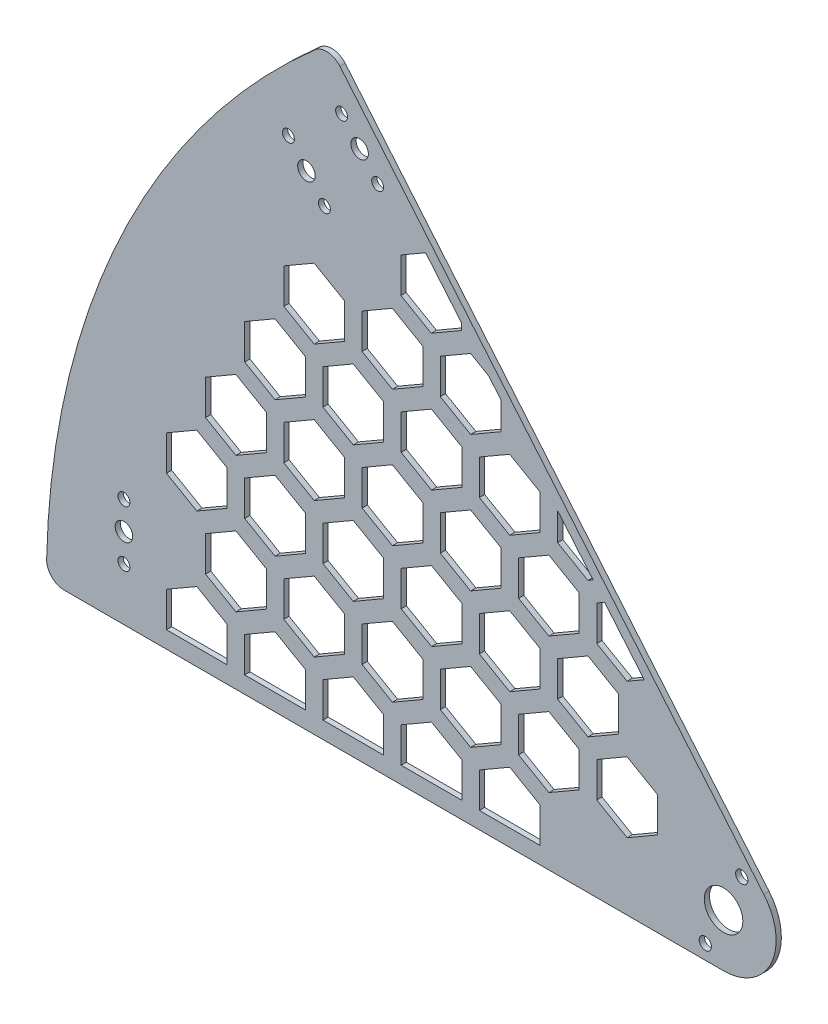
SolidWorks part; units mm, degrees
material "6061 Alloy"
ref_plane "Front Plane" through (0, 0, 0) normal (0, 0, 1) x (1, 0, 0)
ref_plane "Top Plane" through (0, 0, 0) normal (0, 1, 0) x (1, 0, 0)
ref_plane "Right Plane" through (0, 0, 0) normal (1, 0, 0) x (0, 0, -1)
sketch "Sketch1" plane through (0, 0, 0) normal (0, 0, 1) x (1, 0, 0)
  line L0 (22.9813, 19.2836) -> (-218.8588, 307.4975)
  line L1 (0, -30) -> (-376.2365, -30)
  arc A1 (-386.234, -19.7731) -> (-233.1193, 308.5823) centre (64.3352, -30) cw
  circle A2 centre (0, 0) radius 11
  circle A3 centre (0, 0) radius 65 construction
  circle A4 centre (-166.0606, 81.5406) radius 120 construction
  arc A6 (-376.2365, -30) -> (-386.234, -19.7731) centre (-376.2365, -20) cw
  arc A7 (-233.1193, 308.5823) -> (-218.8588, 307.4975) centre (-226.5193, 301.0697) cw
  circle A9 centre (-207.6577, 272.3684) radius 5
  circle A10 centre (0, 0) radius 342.5 construction
  circle A11 centre (-237.9967, 246.3003) radius 5
  circle A12 centre (-342.1261, 16) radius 5
  circle A13 centre (-248.2813, 258.557) radius 3.4 construction
  circle A14 centre (-227.7121, 234.0436) radius 3.4 construction
  circle A15 centre (-197.3731, 260.1117) radius 3.4 construction
  circle A16 centre (-217.9423, 284.6251) radius 3.4 construction
  circle A17 centre (-248.2813, 258.557) radius 3.4
  circle A18 centre (-227.7121, 234.0436) radius 3.4
  circle A19 centre (-197.3731, 260.1117) radius 3.4
  circle A20 centre (-217.9423, 284.6251) radius 3.4
  circle A21 centre (-342.1261, 0) radius 3.4 construction
  circle A22 centre (-342.1261, 32) radius 3.4 construction
  circle A23 centre (-342.1261, 0) radius 3.4
  circle A24 centre (-342.1261, 32) radius 3.4
  arc A27 (-165.8903, -30) -> (-83.6509, 146.363) centre (0, 0) cw construction
  arc A28 (22.9813, 19.2836) -> (0, -30) centre (0, 0) cw
  point P26 (-386.35, -30)
  dimension "D1" = 22
  dimension "D2" = 240
  dimension "D3" = 130
  dimension "D7" = 10
  dimension "D8" = 10
  dimension "D10" = 10
  dimension "D9" = 685
  dimension "D13" = 10
  dimension "D14" = 111.5406
  dimension "D19" = 168.5811
  dimension "D17" = 450.6852
  dimension "D5" = 50
  dimension "D6" = 386.35
  dimension "D11" = 40
  dimension "D12" = 14
extrude "Boss-Extrude1" add sketch "Sketch1" along normal blind 3
sketch "Sketch2" plane through (0, 0, 3) normal (0, 0, 1) x (1, 0, 0)
  line L344 (-45.2594, 91.2285) -> (-67.8697, 118.1744)
  line L378 (-260.9062, 18.2718) -> (-260.9062, 38.2718)
  line L380 (-283.2267, -20.3885) -> (-283.2267, -0.3885)
  line L420 (-283.2267, -0.3885) -> (-300.5472, 9.6115)
  line L428 (-300.5472, 9.6115) -> (-317.8677, -0.3885)
  line L450 (-317.8677, -0.3885) -> (-317.8677, -20.3885)
  line L541 (-376.2365, -30) -> (0, -30) construction
  line L596 (-104.6626, -20.3885) -> (-139.3037, -20.3885)
  line L597 (-260.9062, 38.2718) -> (-278.2267, 48.2718)
  line L598 (-278.2267, 48.2718) -> (-295.5472, 38.2718)
  line L599 (-295.5472, 38.2718) -> (-295.5472, 18.2718)
  line L618 (-295.5472, 18.2718) -> (-278.2267, 8.2718)
  line L633 (-278.2267, 8.2718) -> (-260.9062, 18.2718)
  line L638 (-238.5857, 56.932) -> (-238.5857, 76.932)
  line L643 (-238.5857, 76.932) -> (-255.9062, 86.932)
  line L646 (-255.9062, 86.932) -> (-273.2267, 76.932)
  line L648 (-273.2267, 76.932) -> (-273.2267, 56.932)
  line L649 (-273.2267, 56.932) -> (-255.9062, 46.932)
  line L650 (-255.9062, 46.932) -> (-238.5857, 56.932)
  line L651 (-216.2652, 95.5923) -> (-216.2652, 115.5923)
  line L657 (-216.2652, 115.5923) -> (-233.5857, 125.5923)
  line L665 (-233.5857, 125.5923) -> (-250.9062, 115.5923)
  line L671 (-250.9062, 115.5923) -> (-250.9062, 95.5923)
  line L675 (-250.9062, 95.5923) -> (-233.5857, 85.5923)
  line L693 (-233.5857, 85.5923) -> (-216.2652, 95.5923)
  line L694 (-193.9447, 134.2525) -> (-193.9447, 154.2525)
  line L695 (-193.9447, 154.2525) -> (-211.2652, 164.2525)
  line L696 (-211.2652, 164.2525) -> (-228.5857, 154.2525)
  line L697 (-228.5857, 154.2525) -> (-228.5857, 134.2525)
  line L698 (-228.5857, 134.2525) -> (-211.2652, 124.2525)
  line L699 (-211.2652, 124.2525) -> (-193.9447, 134.2525)
  line L700 (-171.6242, 172.9128) -> (-171.6242, 192.9128)
  line L701 (-171.6242, 192.9128) -> (-188.9447, 202.9128)
  line L702 (-188.9447, 202.9128) -> (-206.2652, 192.9128)
  line L703 (-206.2652, 192.9128) -> (-206.2652, 172.9128)
  line L704 (-206.2652, 172.9128) -> (-188.9447, 162.9128)
  line L705 (-188.9447, 162.9128) -> (-171.6242, 172.9128)
  line L706 (-216.2652, 18.2718) -> (-216.2652, 38.2718)
  line L707 (-216.2652, 38.2718) -> (-233.5857, 48.2718)
  line L708 (-233.5857, 48.2718) -> (-250.9062, 38.2718)
  line L709 (-250.9062, 38.2718) -> (-250.9062, 18.2718)
  line L710 (-250.9062, 18.2718) -> (-233.5857, 8.2718)
  line L711 (-233.5857, 8.2718) -> (-216.2652, 18.2718)
  line L712 (-193.9447, 56.932) -> (-193.9447, 76.932)
  line L713 (-193.9447, 76.932) -> (-211.2652, 86.932)
  line L714 (-211.2652, 86.932) -> (-228.5857, 76.932)
  line L715 (-228.5857, 76.932) -> (-228.5857, 56.932)
  line L716 (-228.5857, 56.932) -> (-211.2652, 46.932)
  line L717 (-211.2652, 46.932) -> (-193.9447, 56.932)
  line L718 (-171.6242, 95.5923) -> (-171.6242, 115.5923)
  line L719 (-171.6242, 115.5923) -> (-188.9447, 125.5923)
  line L720 (-188.9447, 125.5923) -> (-206.2652, 115.5923)
  line L721 (-206.2652, 115.5923) -> (-206.2652, 95.5923)
  line L722 (-206.2652, 95.5923) -> (-188.9447, 85.5923)
  line L723 (-188.9447, 85.5923) -> (-171.6242, 95.5923)
  line L724 (-149.3037, 134.2525) -> (-149.3037, 154.2525)
  line L725 (-149.3037, 154.2525) -> (-166.6242, 164.2525)
  line L726 (-166.6242, 164.2525) -> (-183.9447, 154.2525)
  line L727 (-183.9447, 154.2525) -> (-183.9447, 134.2525)
  line L728 (-183.9447, 134.2525) -> (-166.6242, 124.2525)
  line L729 (-166.6242, 124.2525) -> (-149.3037, 134.2525)
  line L730 (-126.9832, 172.9128) -> (-126.9832, 188.6231)
  line L731 (-133.965, 196.9437) -> (-144.3037, 202.9128)
  line L732 (-144.3037, 202.9128) -> (-161.6242, 192.9128)
  line L733 (-161.6242, 192.9128) -> (-161.6242, 172.9128)
  line L734 (-161.6242, 172.9128) -> (-144.3037, 162.9128)
  line L735 (-144.3037, 162.9128) -> (-126.9832, 172.9128)
  line L736 (-171.6242, 18.2718) -> (-171.6242, 38.2718)
  line L737 (-171.6242, 38.2718) -> (-188.9447, 48.2718)
  line L738 (-188.9447, 48.2718) -> (-206.2652, 38.2718)
  line L739 (-206.2652, 38.2718) -> (-206.2652, 18.2718)
  line L740 (-206.2652, 18.2718) -> (-188.9447, 8.2718)
  line L741 (-188.9447, 8.2718) -> (-171.6242, 18.2718)
  line L742 (-149.3037, 56.932) -> (-149.3037, 76.932)
  line L743 (-149.3037, 76.932) -> (-166.6242, 86.932)
  line L744 (-166.6242, 86.932) -> (-183.9447, 76.932)
  line L745 (-183.9447, 76.932) -> (-183.9447, 56.932)
  line L746 (-183.9447, 56.932) -> (-166.6242, 46.932)
  line L747 (-166.6242, 46.932) -> (-149.3037, 56.932)
  line L748 (-126.9832, 95.5923) -> (-126.9832, 115.5923)
  line L749 (-126.9832, 115.5923) -> (-144.3037, 125.5923)
  line L750 (-144.3037, 125.5923) -> (-161.6242, 115.5923)
  line L751 (-161.6242, 115.5923) -> (-161.6242, 95.5923)
  line L752 (-161.6242, 95.5923) -> (-144.3037, 85.5923)
  line L753 (-144.3037, 85.5923) -> (-126.9832, 95.5923)
  line L754 (-104.6626, 134.2525) -> (-104.6626, 154.2525)
  line L755 (-104.6626, 154.2525) -> (-121.9832, 164.2525)
  line L756 (-121.9832, 164.2525) -> (-139.3037, 154.2525)
  line L757 (-139.3037, 154.2525) -> (-139.3037, 134.2525)
  line L758 (-139.3037, 134.2525) -> (-121.9832, 124.2525)
  line L759 (-121.9832, 124.2525) -> (-104.6626, 134.2525)
  line L766 (-126.9832, 18.2718) -> (-126.9832, 38.2718)
  line L767 (-126.9832, 38.2718) -> (-144.3037, 48.2718)
  line L768 (-144.3037, 48.2718) -> (-161.6242, 38.2718)
  line L769 (-161.6242, 38.2718) -> (-161.6242, 18.2718)
  line L770 (-161.6242, 18.2718) -> (-144.3037, 8.2718)
  line L771 (-144.3037, 8.2718) -> (-126.9832, 18.2718)
  line L772 (-104.6626, 56.932) -> (-104.6626, 76.932)
  line L773 (-104.6626, 76.932) -> (-121.9832, 86.932)
  line L774 (-121.9832, 86.932) -> (-139.3037, 76.932)
  line L775 (-139.3037, 76.932) -> (-139.3037, 56.932)
  line L776 (-139.3037, 56.932) -> (-121.9832, 46.932)
  line L777 (-121.9832, 46.932) -> (-104.6626, 56.932)
  line L778 (-82.3421, 95.5923) -> (-82.3421, 115.5923)
  line L779 (-82.3421, 115.5923) -> (-99.6626, 125.5923)
  line L780 (-99.6626, 125.5923) -> (-116.9832, 115.5923)
  line L781 (-116.9832, 115.5923) -> (-116.9832, 95.5923)
  line L782 (-116.9832, 95.5923) -> (-99.6626, 85.5923)
  line L783 (-99.6626, 85.5923) -> (-82.3421, 95.5923)
  line L787 (-94.6626, 150.1051) -> (-94.6626, 134.2525)
  line L788 (-94.6626, 134.2525) -> (-77.3421, 124.2525)
  line L789 (-77.3421, 124.2525) -> (-74.3967, 125.9531)
  line L796 (-82.3421, 18.2718) -> (-82.3421, 38.2718)
  line L797 (-82.3421, 38.2718) -> (-99.6626, 48.2718)
  line L798 (-99.6626, 48.2718) -> (-116.9832, 38.2718)
  line L799 (-116.9832, 38.2718) -> (-116.9832, 18.2718)
  line L800 (-116.9832, 18.2718) -> (-99.6626, 8.2718)
  line L801 (-99.6626, 8.2718) -> (-82.3421, 18.2718)
  line L802 (-60.0216, 56.932) -> (-60.0216, 76.932)
  line L803 (-60.0216, 76.932) -> (-77.3421, 86.932)
  line L804 (-77.3421, 86.932) -> (-94.6626, 76.932)
  line L805 (-94.6626, 76.932) -> (-94.6626, 56.932)
  line L806 (-94.6626, 56.932) -> (-77.3421, 46.932)
  line L807 (-77.3421, 46.932) -> (-60.0216, 56.932)
  line L810 (-67.8697, 118.1744) -> (-72.3421, 115.5923)
  line L811 (-72.3421, 115.5923) -> (-72.3421, 95.5923)
  line L812 (-72.3421, 95.5923) -> (-55.0216, 85.5923)
  line L813 (-55.0216, 85.5923) -> (-45.2594, 91.2285)
  line L826 (-238.5857, -20.3885) -> (-238.5857, -0.3885)
  line L827 (-238.5857, -0.3885) -> (-255.9062, 9.6115)
  line L828 (-255.9062, 9.6115) -> (-273.2267, -0.3885)
  line L829 (-273.2267, -0.3885) -> (-273.2267, -20.3885)
  line L832 (-193.9447, -20.3885) -> (-193.9447, -0.3885)
  line L833 (-193.9447, -0.3885) -> (-211.2652, 9.6115)
  line L834 (-211.2652, 9.6115) -> (-228.5857, -0.3885)
  line L835 (-228.5857, -0.3885) -> (-228.5857, -20.3885)
  line L838 (-149.3037, -20.3885) -> (-149.3037, -0.3885)
  line L839 (-149.3037, -0.3885) -> (-166.6242, 9.6115)
  line L840 (-166.6242, 9.6115) -> (-183.9447, -0.3885)
  line L841 (-183.9447, -0.3885) -> (-183.9447, -20.3885)
  line L844 (-104.6626, -20.3885) -> (-104.6626, -0.3885)
  line L845 (-104.6626, -0.3885) -> (-121.9832, 9.6115)
  line L846 (-121.9832, 9.6115) -> (-139.3037, -0.3885)
  line L847 (-139.3037, -0.3885) -> (-139.3037, -20.3885)
  line L850 (-283.2267, 56.932) -> (-283.2267, 76.932)
  line L851 (-283.2267, 76.932) -> (-300.5472, 86.932)
  line L852 (-300.5472, 86.932) -> (-317.8677, 76.932)
  line L853 (-317.8677, 76.932) -> (-317.8677, 56.932)
  line L854 (-317.8677, 56.932) -> (-300.5472, 46.932)
  line L855 (-300.5472, 46.932) -> (-283.2267, 56.932)
  line L856 (-260.9062, 95.5923) -> (-260.9062, 115.5923)
  line L857 (-260.9062, 115.5923) -> (-278.2267, 125.5923)
  line L858 (-278.2267, 125.5923) -> (-295.5472, 115.5923)
  line L859 (-295.5472, 115.5923) -> (-295.5472, 95.5923)
  line L860 (-295.5472, 95.5923) -> (-278.2267, 85.5923)
  line L861 (-278.2267, 85.5923) -> (-260.9062, 95.5923)
  line L862 (-238.5857, 134.2525) -> (-238.5857, 154.2525)
  line L863 (-238.5857, 154.2525) -> (-255.9062, 164.2525)
  line L864 (-255.9062, 164.2525) -> (-273.2267, 154.2525)
  line L865 (-273.2267, 154.2525) -> (-273.2267, 134.2525)
  line L866 (-273.2267, 134.2525) -> (-255.9062, 124.2525)
  line L867 (-255.9062, 124.2525) -> (-238.5857, 134.2525)
  line L874 (-216.2652, 172.9128) -> (-216.2652, 192.9128)
  line L875 (-216.2652, 192.9128) -> (-233.5857, 202.9128)
  line L876 (-233.5857, 202.9128) -> (-250.9062, 192.9128)
  line L877 (-250.9062, 192.9128) -> (-250.9062, 172.9128)
  line L878 (-250.9062, 172.9128) -> (-233.5857, 162.9128)
  line L879 (-233.5857, 162.9128) -> (-216.2652, 172.9128)
  line L880 (-305.5472, 18.2718) -> (-305.5472, 38.2718) [skipped]
  line L881 (-305.5472, 38.2718) -> (-322.8677, 48.2718) [skipped]
  line L882 (-322.8677, 48.2718) -> (-340.1882, 38.2718) [skipped]
  line L883 (-340.1882, 38.2718) -> (-340.1882, 18.2718) [skipped]
  line L884 (-340.1882, 18.2718) -> (-322.8677, 8.2718) [skipped]
  line L885 (-322.8677, 8.2718) -> (-305.5472, 18.2718) [skipped]
  line L886 (-37.7011, 172.9128) -> (-37.7011, 192.9128) [skipped]
  line L887 (-37.7011, 192.9128) -> (-55.0216, 202.9128) [skipped]
  line L888 (-55.0216, 202.9128) -> (-72.3421, 192.9128) [skipped]
  line L889 (-72.3421, 192.9128) -> (-72.3421, 172.9128) [skipped]
  line L892 (6.9399, 172.9128) -> (6.9399, 192.9128) [skipped]
  line L893 (6.9399, 192.9128) -> (-10.3806, 202.9128) [skipped]
  line L894 (-10.3806, 202.9128) -> (-27.7011, 192.9128) [skipped]
  line L895 (-27.7011, 192.9128) -> (-27.7011, 172.9128) [skipped]
  line L898 (-15.3806, 134.2525) -> (-15.3806, 154.2525) [skipped]
  line L899 (-15.3806, 154.2525) -> (-32.7011, 164.2525) [skipped]
  line L900 (-32.7011, 164.2525) -> (-50.0216, 154.2525) [skipped]
  line L901 (-50.0216, 154.2525) -> (-50.0216, 134.2525) [skipped]
  line L904 (-82.3421, 172.9128) -> (-82.3421, 192.9128) [skipped]
  line L905 (-82.3421, 192.9128) -> (-99.6626, 202.9128) [skipped]
  line L906 (-99.6626, 202.9128) -> (-116.9832, 192.9128) [skipped]
  line L907 (-116.9832, 192.9128) -> (-116.9832, 172.9128) [skipped]
  line L910 (-149.4832, 211.6767) -> (-149.4832, 215.4376)
  line L912 (-169.9676, 239.85) -> (-184.1242, 231.6767)
  line L913 (-184.1242, 231.6767) -> (-184.1242, 211.6767)
  line L914 (-184.1242, 211.6767) -> (-166.8037, 201.6767)
  line L915 (-166.8037, 201.6767) -> (-149.4832, 211.6767)
  line L916 (-37.7011, 18.2718) -> (-37.7011, 38.2718)
  line L917 (-37.7011, 38.2718) -> (-55.0216, 48.2718)
  line L918 (-55.0216, 48.2718) -> (-72.3421, 38.2718)
  line L919 (-72.3421, 38.2718) -> (-72.3421, 18.2718)
  line L920 (-72.3421, 18.2718) -> (-55.0216, 8.2718)
  line L921 (-55.0216, 8.2718) -> (-37.7011, 18.2718)
  line L922 (-149.4832, 231.6767) -> (-166.8037, 241.6767) [skipped]
  line L923 (-77.3421, 164.2525) -> (-94.6626, 154.2525) [skipped]
  line L924 (-37.7011, 95.5923) -> (-37.7011, 115.5923) [skipped]
  line L925 (-37.7011, 115.5923) -> (-55.0216, 125.5923) [skipped]
  line L926 (-60.0216, 134.2525) -> (-60.0216, 154.2525) [skipped]
  line L927 (-60.0216, 154.2525) -> (-77.3421, 164.2525) [skipped]
  line L928 (-317.8677, -20.3885) -> (-309.2075, -25.3885) [skipped]
  line L929 (-291.8869, -25.3885) -> (-283.2267, -20.3885) [skipped]
  line L930 (-149.4832, 215.4376) -> (-169.9676, 239.85)
  line L931 (-126.9832, 188.6231) -> (-133.965, 196.9437)
  line L932 (-74.3967, 125.9531) -> (-94.6626, 150.1051)
  line L933 (-283.2267, -20.3885) -> (-317.8677, -20.3885)
  line L934 (-238.5857, -20.3885) -> (-273.2267, -20.3885)
  line L935 (-193.9447, -20.3885) -> (-228.5857, -20.3885)
  line L936 (-149.3037, -20.3885) -> (-183.9447, -20.3885)
  line L937 (-418.4912, -20.3885) -> (48.3984, -20.3885) construction
  line L938 (48.3984, -20.3885) -> (-228.853, 310.0269) construction
  arc A0 (-286.4051, -20.3885) -> (-314.6894, -20.3885) centre (-300.5472, -10.3885) ccw construction
  point P2 (-82.3421, 28.2718)
  point P151 (-219.9254, 51.932)
  dimension "D1" = 50
  dimension "D4" = 6
  dimension "D5" = 10
  dimension "D6" = 10
  dimension "D3" = 5
  dimension "D8" = 104.6626
  dimension "D9" = 2
  dimension "D10" = 10
  dimension "D11" = 2
  dimension "D13" = 2
  dimension "D15" = 10
  dimension "D16" = 20
  dimension "D17" = 20
  dimension "D18" = 10
  dimension "D2" = 20
  dimension "D7" = 10
  dimension "D12" = 10.1795
  dimension "D14" = 10
  dimension "D19" = 34.641
  dimension "D20" = 44.641
  dimension "D21" = 120
  dimension "D22" = 20
  dimension "D23" = 15.7103
  dimension "D24" = 3.4011
  dimension "D25" = 44.641
  dimension "D26" = 120
  dimension "D27" = 20
  dimension "D28" = 120
  dimension "D29" = 11.2725
  dimension "D30" = 20
  dimension "D31" = 120
  dimension "D32" = 20
  dimension "D33" = 20
  dimension "D34" = 31.8681
extrude "Cut-Extrude1" cut sketch "Sketch2" against normal up to surface (3 mm away) up to face at (-338.7261, 0, 0)
sketch "Sketch3" plane through (0, 0, 0) normal (0, 0, -1) x (-1, 0, 0)
  circle A8 centre (-10.4048, 21.6273) radius 3.5
  circle A9 centre (10.4048, -21.6273) radius 3.5
  dimension "D1" = 7
  dimension "D2" = 7
extrude "Cut-Extrude2" cut sketch "Sketch3" against normal through all
